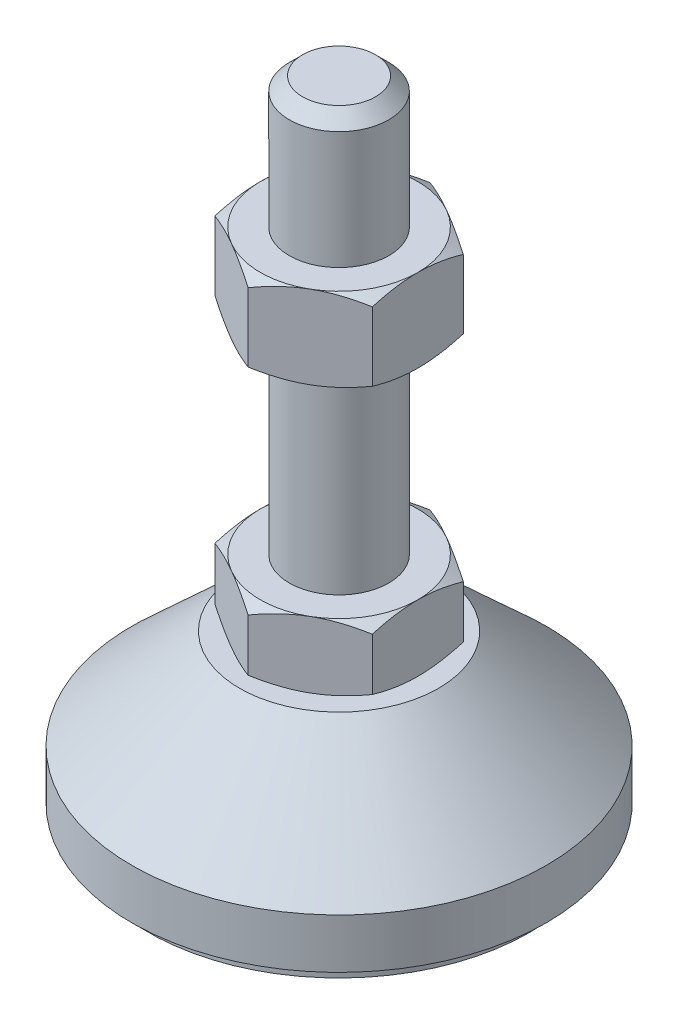
SolidWorks part; units mm, degrees
ref_plane "Спереди" through (0, 0, 0) normal (0, 0, 1) x (1, 0, 0)
ref_plane "Сверху" through (0, 0, 0) normal (0, 1, 0) x (1, 0, 0)
ref_plane "Справа" through (0, 0, 0) normal (1, 0, 0) x (0, 0, -1)
sketch "Эскиз1" plane through (0, 0, 0) normal (0, 0, 1) x (1, 0, 0)
  line L0 (0, 0) -> (-23, 0)
  line L1 (-23, 0) -> (-23, 2)
  line L2 (-23, 2) -> (-25, 2)
  line L3 (-25, 2) -> (-25, 8)
  line L4 (-25, 8) -> (-12, 20)
  line L5 (-12, 20) -> (-6, 20)
  line L12 (-6, 28) -> (-6, 76.4)
  line L13 (-6, 76.4) -> (-4.4, 78)
  line L14 (-4.4, 78) -> (0, 78)
  line L15 (0, 78) -> (0, 0) construction
  line L16 (-6, 20) -> (0, 20) construction
  line L17 (0, 0) -> (0, 78)
  line L18 (0, 0) -> (0, -7.9595) construction
  line L19 (-6, 28) -> (-6, 20)
  point P8 (-6, 52.2)
  point P23 (-9, 20)
  dimension "D1" = 12
  dimension "D2" = 20
  dimension "D3" = 8
  dimension "D4" = 50
  dimension "D5" = 6
  dimension "D6" = 1.6
  dimension "D7" = 45
  dimension "D8" = 24
  dimension "D9" = 2
  dimension "D10" = 50
  dimension "D11" = 6
revolve "Повернуть1" add sketch "Эскиз1" angle 360 about L17
sketch "Эскиз2" plane through (0, 20, 0) normal (0, 1, 0) x (1, 0, 0)
  line L1 (0, 10.9697) -> (-9.5, 5.4848)
  line L2 (-9.5, 5.4848) -> (-9.5, -5.4848)
  line L3 (-9.5, -5.4848) -> (0, -10.9697)
  line L4 (0, -10.9697) -> (9.5, -5.4848)
  line L5 (9.5, -5.4848) -> (9.5, 5.4848)
  line L6 (9.5, 5.4848) -> (0, 10.9697)
  circle A0 centre (0, 0) radius 9.5 construction
  dimension "D1" = 19
extrude "Бобышка-Вытянуть1" add sketch "Эскиз2" along normal up to vertex (8 mm away) up to point (-6, 28, 0)
ref_plane "Плоскость1" through (0, 52.2, 0) normal (0, 1, 0) x (1, 0, 0)
sketch "Эскиз3" plane through (0, 52.2, 0) normal (0, 1, 0) x (1, 0, 0)
  line L6 (9.5, 5.4848) -> (0, 10.9697)
  line L7 (0, 10.9697) -> (-9.5, 5.4848)
  line L8 (-9.5, 5.4848) -> (-9.5, -5.4848)
  line L9 (-9.5, -5.4848) -> (0, -10.9697)
  line L10 (0, -10.9697) -> (9.5, -5.4848)
  line L11 (9.5, -5.4848) -> (9.5, 5.4848)
  line L12 (9.5, 5.4848) -> (0, 10.9697)
  line L13 (0, 10.9697) -> (-9.5, 5.4848)
  line L14 (-9.5, 5.4848) -> (-9.5, -5.4848)
  line L15 (-9.5, -5.4848) -> (0, -10.9697)
  line L16 (0, -10.9697) -> (9.5, -5.4848)
  line L17 (9.5, -5.4848) -> (9.5, 5.4848)
  dimension "D1" = 0
extrude "Бобышка-Вытянуть2" add sketch "Эскиз3" along normal blind 10
sketch "Эскиз4" plane through (0, 0, 0) normal (0, 0, 1) x (1, 0, 0)
  line L0 (-9.5, 62.2) -> (-18.1603, 57.2)
  line L1 (-18.1603, 57.2) -> (-18.1603, 62.2)
  line L2 (-18.1603, 62.2) -> (-9.5, 62.2)
  line L3 (-18.1603, 57.2) -> (-9.5, 52.2)
  line L4 (50, 52.2) -> (-50, 52.2) construction
  line L5 (-9.5, 52.2) -> (-18.1603, 52.2)
  line L6 (-18.1603, 52.2) -> (-18.1603, 57.2)
  line L7 (-9.5, 62.2) -> (-9.5, 52.2) construction
  line L8 (-9.5, 28) -> (-16.4282, 28)
  line L9 (-16.4282, 28) -> (-16.4282, 24)
  line L10 (-16.4282, 24) -> (-9.5, 28)
  line L11 (-9.5, 20) -> (-16.4282, 24)
  line L12 (-16.4282, 24) -> (-16.4282, 20)
  line L13 (-16.4282, 20) -> (-9.5, 20)
  line L14 (0, 78) -> (0, 96.3793) construction
  dimension "D1" = 30
  dimension "D2" = 30
revolve "Вырез-Повернуть2" cut sketch "Эскиз4" angle 360 about L14
